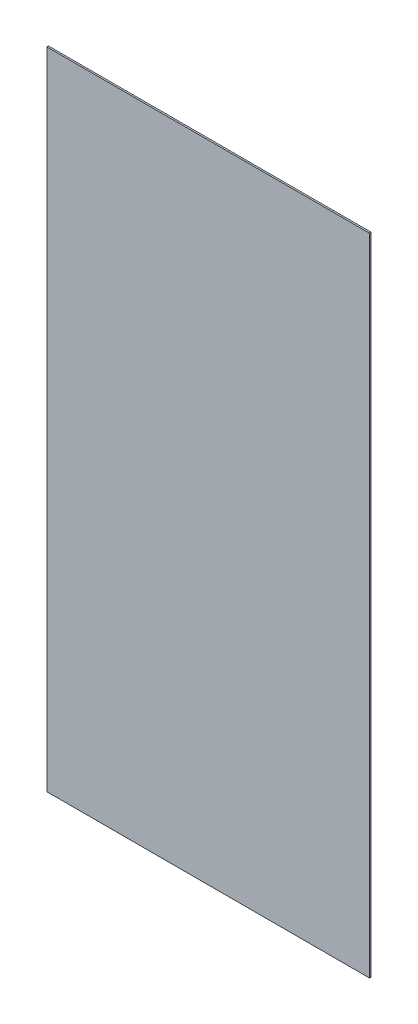
SolidWorks part; units mm, degrees
material "AISI 1020"
ref_plane "Front Plane" through (0, 0, 0) normal (0, 0, 1) x (1, 0, 0)
ref_plane "Top Plane" through (0, 0, 0) normal (0, 1, 0) x (1, 0, 0)
ref_plane "Right Plane" through (0, 0, 0) normal (1, 0, 0) x (0, 0, -1)
sketch "Sketch1" plane through (0, 0, 0) normal (0, 0, 1) x (1, 0, 0)
  line L1 (-15, 30) -> (15, 30)
  line L2 (-15, 30) -> (-15, -30)
  line L3 (-15, -30) -> (15, -30)
  line L4 (15, 30) -> (15, -30)
  line L5 (-15, 30) -> (15, -30) construction
  line L6 (-15, -30) -> (15, 30) construction
  point P0 (0, 0)
  dimension "D1" = 30
  dimension "D2" = 60
extrude "Boss-Extrude1" add sketch "Sketch1" along normal blind 0.15
